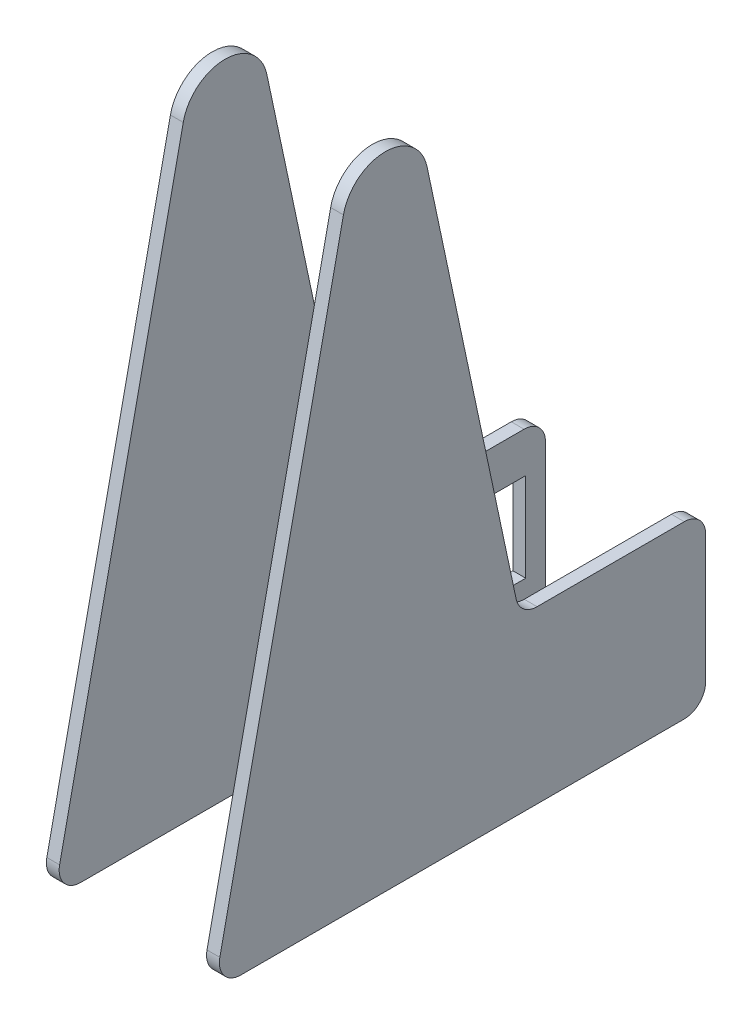
SolidWorks part; units mm, degrees
ref_plane "Front Plane" through (0, 0, 0) normal (0, 0, 1) x (1, 0, 0)
ref_plane "Top Plane" through (0, 0, 0) normal (0, 1, 0) x (1, 0, 0)
ref_plane "Right Plane" through (0, 0, 0) normal (1, 0, 0) x (0, 0, -1)
sketch "nodal" plane through (0, 0, 0) normal (1, 0, 0) x (0, 0, -1)
  line L0 (0, 0) -> (60, 0) construction
  line L1 (0, 0) -> (0, 140) construction
  line L2 (0, 0) -> (60, 0)
  line L3 (0, 0) -> (0, 140)
  line L4 (60, 0) -> (60, 20) construction
  line L5 (60, 0) -> (60, 20)
sketch "motor mount holes" plane through (0, 0, 0) normal (1, 0, 0) x (0, 0, -1)
  arc A40 (74.05, 17) -> (74.05, 13) centre (74.05, 15) ccw construction
  arc A41 (25.55, 13) -> (25.55, 17) centre (25.55, 15) ccw construction
  arc A42 (74.05, 27) -> (74.05, 23) centre (74.05, 25) ccw construction
  arc A43 (25.55, 23) -> (25.55, 27) centre (25.55, 25) ccw construction
  arc A44 (74.05, 17) -> (74.05, 13) centre (74.05, 15) ccw construction
  arc A45 (25.55, 13) -> (25.55, 17) centre (25.55, 15) ccw construction
  arc A46 (74.05, 27) -> (74.05, 23) centre (74.05, 25) ccw construction
  arc A47 (25.55, 23) -> (25.55, 27) centre (25.55, 25) ccw construction
  circle A48 centre (25.55, 25) radius 2
  circle A49 centre (74.05, 25) radius 2
  circle A50 centre (74.05, 15) radius 2
  circle A51 centre (25.55, 15) radius 2
ref_plane "Plane1" through (17.25, 0, 0) normal (1, 0, 0) x (0, 0, -1)
sketch "Sketch3" plane through (17.25, 0, 0) normal (1, 0, 0) x (0, 0, -1)
  line L1 (0, 0) -> (0, 250) construction
  line L2 (-33.8247, 0) -> (0, 0)
  line L3 (0, 0) -> (0, 150) construction
  line L5 (-9.7812, 142.0803) -> (-38.7153, 6.0402)
  line L6 (9.7812, 142.0803) -> (38.7153, 6.0402) construction
  line L7 (35.5409, 40) -> (70, 40)
  line L8 (75, 35) -> (75, 5)
  line L9 (70, 0) -> (0, 0)
  line L10 (9.7812, 142.0803) -> (30.6503, 43.9598)
  circle A0 centre (0, 140) radius 10 construction
  arc A1 (-38.7153, 6.0402) -> (-33.8247, 0) centre (-33.8247, 5) ccw
  arc A2 (35.5409, 40) -> (30.6503, 43.9598) centre (35.5409, 45) cw
  arc A3 (70, 0) -> (75, 5) centre (70, 5) ccw
  arc A4 (75, 35) -> (70, 40) centre (70, 35) ccw
  arc A5 (-9.7812, 142.0803) -> (9.7812, 142.0803) centre (0, 140) cw
  point P13 (-40, 0)
  point P20 (31.4925, 40)
  point P23 (75, 0)
  point P26 (75, 40)
  dimension "D1" = 20
  dimension "D3" = 5
  dimension "D6" = 5
  dimension "D7" = 5
  dimension "D2" = 40
  dimension "D4" = 75
  dimension "D5" = 40
extrude "Boss-Extrude1" add sketch "Sketch3" along normal blind 3 contours A5 L5 A1 L2 L9 A3 L8 A4 L7 A2 L10
mirror "Mirror2" about plane through (0, 0, 0) normal (1, 0, 0) of bodies 101
sketch "motor size" plane through (-20.25, 0, 0) normal (-1, 0, 0) x (0, 0, 1)
  line L0 (-75.05, 30) -> (-69.5, 30) construction
  line L1 (-29.6134, 30) -> (-69.9866, 30) construction
  line L2 (-29.6134, 30) -> (-29.6134, 10) construction
  line L3 (-29.6134, 10) -> (-69.9866, 10) construction
  line L4 (-69.9866, 30) -> (-69.9866, 10) construction
  line L5 (-69.5, 10) -> (-75.05, 10) construction
  line L6 (-29.6134, 10.5) -> (-29.6134, 29.5) construction
  line L7 (-69.9866, 29.5) -> (-69.9866, 10.5) construction
  line L8 (-69.9866, 30) -> (-29.6134, 10) construction
  line L9 (-29.6134, 30) -> (-69.9866, 10) construction
  point P4 (-49.8, 20)
sketch "Sketch5" plane through (-20.25, 0, 0) normal (-1, 0, 0) x (0, 0, 1)
  line L0 (-69.9866, 30) -> (-29.6134, 10) construction
  line L1 (-70.3866, 30.4) -> (-29.2134, 30.4)
  line L2 (-70.3866, 30.4) -> (-70.3866, 9.6)
  line L3 (-70.3866, 9.6) -> (-29.2134, 9.6)
  line L4 (-29.2134, 30.4) -> (-29.2134, 9.6)
  line L5 (-70.3866, 30.4) -> (-29.2134, 9.6) construction
  line L6 (-70.3866, 9.6) -> (-29.2134, 30.4) construction
  line L7 (-29.6134, 30) -> (-69.9866, 30) construction
  line L8 (-29.6134, 30) -> (-29.6134, 10) construction
  point P0 (-49.8, 20)
  dimension "D1" = 0.4
  dimension "D2" = 0.4
extrude "Cut-Extrude1" cut sketch "Sketch5" against normal up to surface (3 mm away) and the other way through all up to face at (-17.25, 46.0048, -28.358)
equation "\"motor center z\" = 60mm"
equation "\"motor center y\" = 20mm"
equation "\"link 1\" = 40mm"
equation "\"link 2\"= 90mm"
equation "\"pivot height\"= 140mm"
equation "\"camera height\" = 250mm"
equation "\"link 1 thickness\" = 6mm"
equation "\"link height\" = 20mm"
equation "\"pivot size\" = 6mm"
equation "\"D2@Sketch3\"=\"motor center z\"*2/3"
equation "\"D4@Sketch3\"=\"motor center z\"*5/4"
equation "\"D5@Sketch3\"=\"motor center y\"*2"
